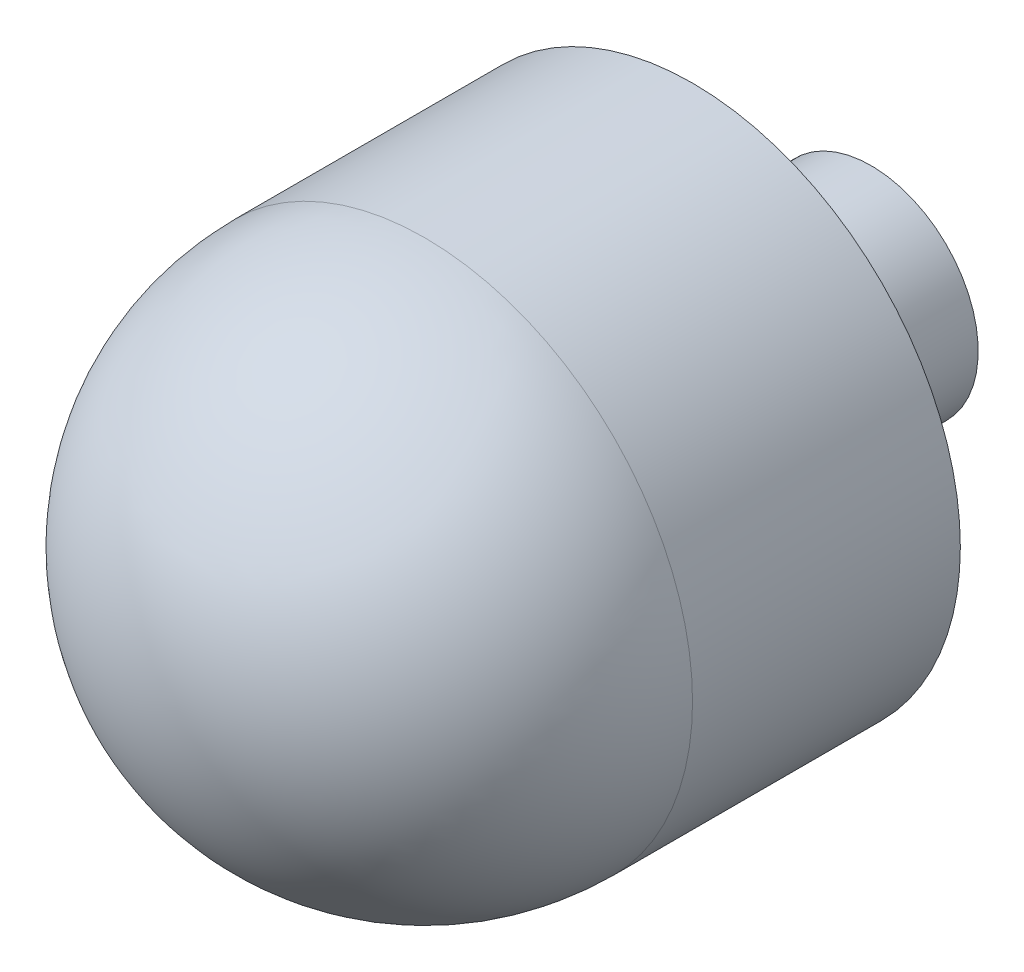
SolidWorks part; units mm, degrees
ref_plane "Front Plane" through (0, 0, 0) normal (0, 0, 1) x (1, 0, 0)
ref_plane "Top Plane" through (0, 0, 0) normal (0, 1, 0) x (1, 0, 0)
ref_plane "Right Plane" through (0, 0, 0) normal (1, 0, 0) x (0, 0, -1)
sketch "Sketch1" plane through (0, 0, 0) normal (0, 1, 0) x (1, 0, 0)
  line L0 (0, 105.1364) -> (0, -75.1364) construction
  line L1 (15, 15) -> (15, 30)
  line L2 (15, 30) -> (6, 30)
  line L3 (6, 30) -> (6, 40)
  line L4 (6, 40) -> (0, 40)
  line L5 (0, 40) -> (0, 0)
  arc A0 (0, 0) -> (15, 15) centre (0, 15) ccw
  dimension "D1" = 15
  dimension "D2" = 25
  dimension "D3" = 10
  dimension "D4" = 6
revolve "Revolve1" add sketch "Sketch1" angle 360 about L0
